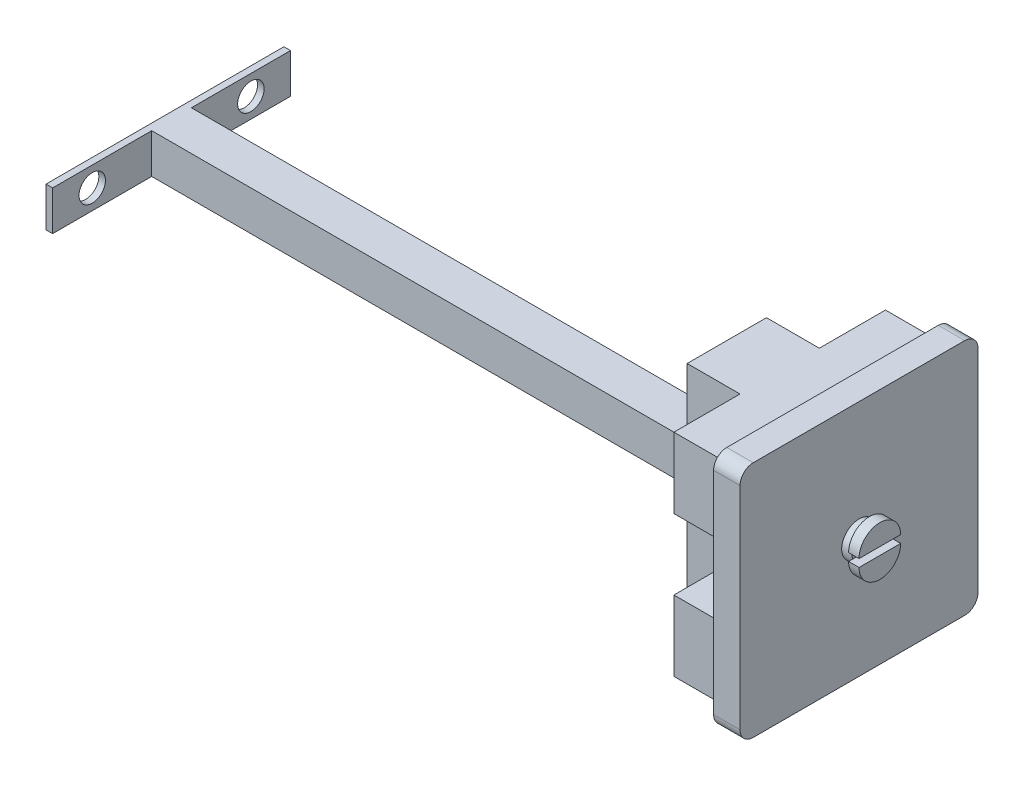
SolidWorks part; units mm, degrees
ref_plane "Front Plane" through (0, 0, 0) normal (0, 0, 1) x (1, 0, 0)
ref_plane "Top Plane" through (0, 0, 0) normal (0, 1, 0) x (1, 0, 0)
ref_plane "Right Plane" through (0, 0, 0) normal (1, 0, 0) x (0, 0, -1)
sketch "Sketch1" plane through (0, 0, 0) normal (1, 0, 0) x (0, 0, -1)
  line L1 (50.8, -9.525) -> (-50.8, -9.525)
  line L2 (50.8, -9.525) -> (50.8, 9.525)
  line L3 (50.8, 9.525) -> (-50.8, 9.525)
  line L4 (-50.8, -9.525) -> (-50.8, 9.525)
  line L5 (50.8, -9.525) -> (-50.8, 9.525) construction
  line L6 (50.8, 9.525) -> (-50.8, -9.525) construction
  point P0 (0, 0)
  dimension "D1" = 101.6
  dimension "D2" = 19.05
extrude "Boss-Extrude1" add sketch "Sketch1" along normal blind 3.175
sketch "Sketch2" plane through (3.175, 0, 0) normal (1, 0, 0) x (0, 0, -1)
  line L0 (50.8, 9.525) -> (-50.8, 9.525) construction
  line L1 (9.525, -9.525) -> (-9.525, -9.525)
  line L2 (9.525, -9.525) -> (9.525, 9.525)
  line L3 (9.525, 9.525) -> (-9.525, 9.525)
  line L4 (-9.525, -9.525) -> (-9.525, 9.525)
  line L5 (9.525, -9.525) -> (-9.525, 9.525) construction
  line L6 (9.525, 9.525) -> (-9.525, -9.525) construction
  point P0 (0, 0)
extrude "Boss-Extrude2" add sketch "Sketch2" along normal blind 266.7
sketch "Sketch3" plane through (269.875, 0, 0) normal (1, 0, 0) x (0, 0, -1)
  line L0 (1.27, -2.54) -> (-1.27, -2.54)
  line L1 (5.08, -6.35) -> (2.54, -6.35)
  line L2 (-5.08, -6.35) -> (-1.27, -2.54)
  line L3 (1.27, -2.54) -> (5.08, -6.35)
  line L4 (0, 0) -> (0, -9.525) construction
  line L5 (-9.525, -9.525) -> (9.525, -9.525) construction
  line L6 (-2.54, -9.525) -> (2.54, -9.525)
  line L7 (2.54, -9.525) -> (2.54, -6.35)
  line L8 (-2.54, -9.525) -> (-2.54, -6.35)
  line L9 (-2.54, -6.35) -> (-5.08, -6.35)
  line L10 (-6.35, -5.08) -> (-6.35, -2.54)
  line L11 (-9.525, -2.54) -> (-6.35, -2.54)
  line L12 (-9.525, 2.54) -> (-9.525, -2.54)
  line L13 (-9.525, 2.54) -> (-6.35, 2.54)
  line L14 (-6.35, 2.54) -> (-6.35, 5.08)
  line L15 (-6.35, 5.08) -> (-2.54, 1.27)
  line L16 (-2.54, -1.27) -> (-2.54, 1.27)
  line L17 (-2.54, -1.27) -> (-6.35, -5.08)
  line L18 (-5.08, 6.35) -> (-2.54, 6.35)
  line L19 (-2.54, 9.525) -> (-2.54, 6.35)
  line L20 (2.54, 9.525) -> (-2.54, 9.525)
  line L21 (2.54, 9.525) -> (2.54, 6.35)
  line L22 (2.54, 6.35) -> (5.08, 6.35)
  line L23 (5.08, 6.35) -> (1.27, 2.54)
  line L24 (-1.27, 2.54) -> (1.27, 2.54)
  line L25 (-1.27, 2.54) -> (-5.08, 6.35)
  line L26 (6.35, 5.08) -> (6.35, 2.54)
  line L27 (9.525, 2.54) -> (6.35, 2.54)
  line L28 (9.525, -2.54) -> (9.525, 2.54)
  line L29 (9.525, -2.54) -> (6.35, -2.54)
  line L30 (6.35, -2.54) -> (6.35, -5.08)
  line L31 (6.35, -5.08) -> (2.54, -1.27)
  line L32 (2.54, 1.27) -> (2.54, -1.27)
  line L33 (2.54, 1.27) -> (6.35, 5.08)
  circle A0 centre (0, 0) radius 3.9132 construction
  point P3 (0, -2.54)
  point P6 (0, -7.62)
  point P16 (0, -9.525)
  point P44 (0, 0)
  dimension "D6" = 4
  dimension "D1" = 2.54
  dimension "D2" = 45
  dimension "D3" = 3.81
  dimension "D4" = 2.54
  dimension "D5" = 5.08
extrude "Cut-Extrude1" [suppressed] cut sketch "Sketch3" against normal blind 266.7
sketch "Sketch4" plane through (269.875, 0, 0) normal (1, 0, 0) x (0, 0, -1)
  line L1 (57.15, -57.15) -> (-57.15, -57.15)
  line L2 (57.15, -57.15) -> (57.15, 57.15)
  line L3 (57.15, 57.15) -> (-57.15, 57.15)
  line L4 (-57.15, -57.15) -> (-57.15, 57.15)
  line L5 (57.15, -57.15) -> (-57.15, 57.15) construction
  line L6 (57.15, 57.15) -> (-57.15, -57.15) construction
  point P0 (0, 0)
  dimension "D1" = 114.3
extrude "Boss-Extrude3" add sketch "Sketch4" along normal blind 76.2
sketch "Sketch5" plane through (0, -57.15, 0) normal (0, -1, 0) x (1, 0, 0)
  line L0 (315.3051, -57.15) -> (315.3051, -19.05) construction
  line L1 (269.875, 57.15) -> (295.275, 57.15)
  line L2 (269.875, 57.15) -> (269.875, 19.05)
  line L3 (269.875, 19.05) -> (295.275, 19.05)
  line L4 (295.275, 57.15) -> (295.275, 19.05)
  line L5 (269.875, -57.15) -> (295.275, -57.15)
  line L6 (269.875, -57.15) -> (269.875, -19.05)
  line L7 (269.875, -19.05) -> (295.275, -19.05)
  line L8 (295.275, -57.15) -> (295.275, -19.05)
  line L9 (346.075, -57.15) -> (269.875, -57.15) construction
  line L10 (315.3051, -19.05) -> (315.3051, 19.05) construction
  line L11 (315.3051, 19.05) -> (315.3051, 57.15) construction
  line L12 (346.075, 57.15) -> (269.875, 57.15) construction
  dimension "D1" = 25.4
extrude "Cut-Extrude2" cut sketch "Sketch5" against normal blind 150.368
sketch "Sketch7" plane through (269.875, 0, 0) normal (-1, 0, 0) x (0, 0, 1)
  line L1 (50.8, -50.8) -> (-50.8, -50.8)
  line L2 (50.8, -50.8) -> (50.8, 50.8)
  line L3 (50.8, 50.8) -> (-50.8, 50.8)
  line L4 (-50.8, -50.8) -> (-50.8, 50.8)
  line L5 (50.8, -50.8) -> (-50.8, 50.8) construction
  line L6 (50.8, 50.8) -> (-50.8, -50.8) construction
  point P0 (0, 0)
  dimension "D1" = 101.6
extrude "Cut-Extrude3" cut sketch "Sketch7" against normal blind 50.8 flip side to cut
sketch "Sketch8" plane through (0, 0, 50.8) normal (0, 0, 1) x (1, 0, 0)
  line L0 (295.275, 50.8) -> (295.275, -50.8) construction
  line L1 (295.275, 16.9333) -> (320.675, 16.9333)
  line L2 (295.275, 16.9333) -> (295.275, -16.9333)
  line L3 (295.275, -16.9333) -> (320.675, -16.9333)
  line L4 (320.675, 16.9333) -> (320.675, -16.9333)
  line L5 (320.675, -57.15) -> (320.675, 57.15) construction
  line L6 (307.975, 50.8) -> (307.975, 16.9333) construction
  line L7 (320.675, 50.8) -> (295.275, 50.8) construction
  line L8 (307.975, 16.9333) -> (307.975, -16.9333) construction
  line L9 (307.975, -16.9333) -> (307.975, -50.8) construction
  line L10 (320.675, -50.8) -> (295.275, -50.8) construction
  line L11 (269.875, 0) -> (295.275, 0) construction
  line L12 (269.875, 9.525) -> (269.875, -9.525) construction
extrude "Cut-Extrude4" cut sketch "Sketch8" against normal blind 140.208
sketch "Sketch9" plane through (346.075, 0, 0) normal (1, 0, 0) x (0, 0, -1)
  line L4 (-57.15, 57.15) -> (-57.15, -57.15)
  line L5 (-57.15, -57.15) -> (57.15, -57.15)
  line L6 (57.15, -57.15) -> (57.15, 57.15)
  line L7 (57.15, 57.15) -> (-57.15, 57.15)
  line L8 (-57.15, 57.15) -> (-57.15, -57.15)
  line L9 (-57.15, -57.15) -> (57.15, -57.15)
  line L10 (57.15, -57.15) -> (57.15, 57.15)
  line L11 (57.15, 57.15) -> (-57.15, 57.15)
  dimension "D1" = 0
extrude "Cut-Extrude5" cut sketch "Sketch9" against normal blind 12.7
fillet "Fillet2" radius 6.35 4 edges at (327.025, -57.15, -57.15) (327.025, 57.15, -57.15) (327.025, -57.15, 57.15) (327.025, 57.15, 57.15)
sketch "Sketch10" plane through (0, 0, 0) normal (-1, 0, 0) x (0, 0, 1)
  line L0 (38.1, 0) -> (-38.1, 0) construction
  circle A0 centre (-38.1, 0) radius 6.35
  circle A1 centre (38.1, 0) radius 6.35
  point P4 (0, 0)
  dimension "D2" = 12.7
  dimension "D1" = 76.2
extrude "Cut-Extrude6" cut sketch "Sketch10" against normal blind 12.7
sketch "Sketch11" plane through (333.375, 0, 0) normal (1, 0, 0) x (0, 0, -1)
  circle A0 centre (0, 0) radius 43.9243
scale "Scale1" scale about centroid uniform scaling yes scale factor 0.06
other "Move Face1" face at (259.0386, 0, -3.048) face at (259.0386, 0, 3.048) parameters "D1"=0.38
sketch "Sketch12" plane through (278.9459, 0, 0) normal (1, 0, 0) x (0, 0, -1)
  circle A0 centre (0, 0) radius 0.5
  dimension "D1" = 1
extrude "Boss-Extrude4" add sketch "Sketch12" along normal blind 0.3
sketch "Sketch13" plane through (279.2459, 0, 0) normal (1, 0, 0) x (0, 0, -1)
  line L0 (0.6, 0) -> (-0.6, 0) construction
  line L1 (-3.048, -3.429) -> (3.048, -3.429) construction
  line L2 (0.6, 0.11) -> (-0.6, 0.11)
  line L3 (0.6, -0.11) -> (-0.6, -0.11)
  arc A1 (-0.6, -0.11) -> (0.6, -0.11) centre (0, -0.11) ccw
  arc A2 (0.6, 0.11) -> (-0.6, 0.11) centre (0, 0.11) ccw
  point P5 (0, 0)
  dimension "D1" = 1.2
  dimension "D2" = 0.11
  dimension "D3" = 0.11
extrude "Boss-Extrude5" add sketch "Sketch13" along normal blind 0.3
